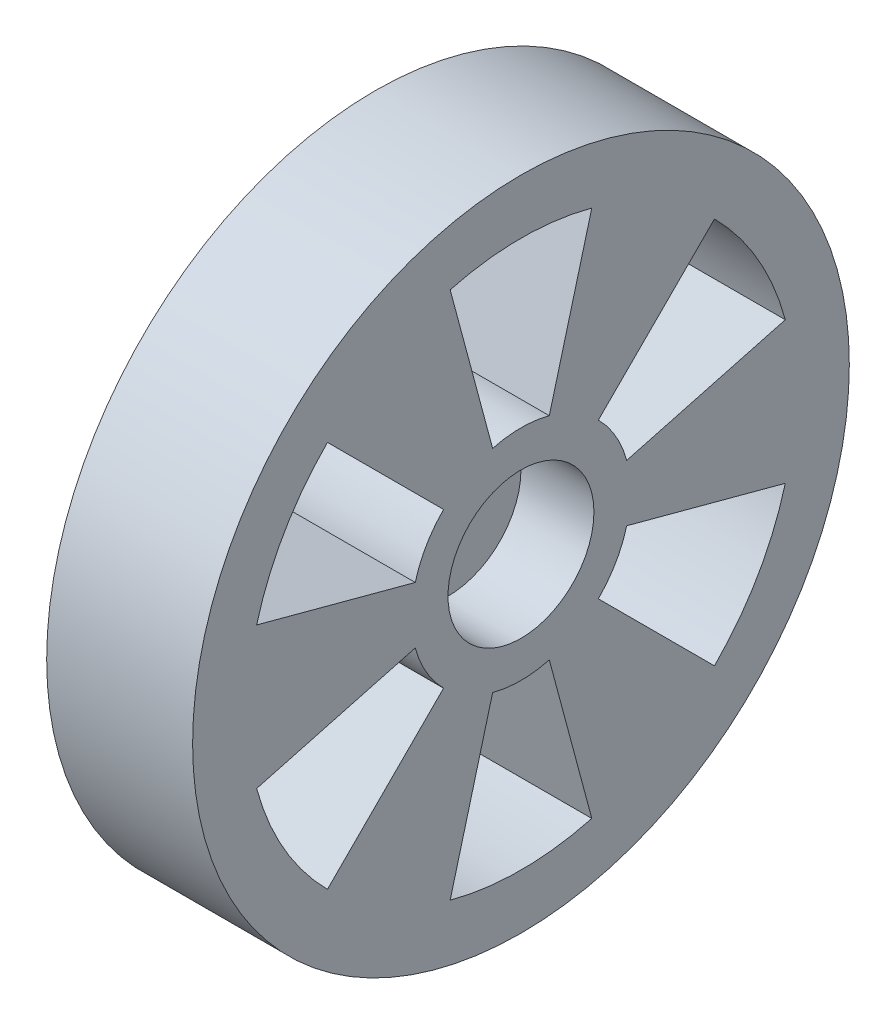
SolidWorks part; units mm, degrees
ref_plane "前视基准面" through (0, 0, 0) normal (0, 0, 1) x (1, 0, 0)
ref_plane "上视基准面" through (0, 0, 0) normal (0, 1, 0) x (1, 0, 0)
ref_plane "右视基准面" through (0, 0, 0) normal (1, 0, 0) x (0, 0, -1)
sketch "草图1" plane through (0, 0, 0) normal (1, 0, 0) x (0, 0, -1)
  circle A0 centre (0, 0) radius 10
extrude "凸台-拉伸1" add sketch "草图1" along normal blind 20
sketch "草图2" plane through (20, 0, 0) normal (1, 0, 0) x (0, 0, -1)
  circle A0 centre (0, 0) radius 45
extrude "凸台-拉伸2" add sketch "草图2" along normal blind 20
sketch "草图3" plane through (20, 0, 0) normal (-1, 0, 0) x (0, 0, 1)
  line L0 (0, 37.5) -> (0, 15) construction
  line L1 (-9.7057, 36.2222) -> (-3.8823, 14.4889)
  line L2 (9.7057, 36.2222) -> (3.8823, 14.4889)
  line L3 (0, -15) -> (0, -37.5) construction
  line L4 (26.5165, 26.5165) -> (10.6066, 10.6066)
  line L5 (36.2222, 9.7057) -> (14.4889, 3.8823)
  line L6 (36.2222, -9.7057) -> (14.4889, -3.8823)
  line L7 (26.5165, -26.5165) -> (10.6066, -10.6066)
  line L8 (9.7057, -36.2222) -> (3.8823, -14.4889)
  line L9 (-9.7057, -36.2222) -> (-3.8823, -14.4889)
  line L10 (-26.5165, -26.5165) -> (-10.6066, -10.6066)
  line L11 (-36.2222, -9.7057) -> (-14.4889, -3.8823)
  line L12 (-36.2222, 9.7057) -> (-14.4889, 3.8823)
  line L13 (-26.5165, 26.5165) -> (-10.6066, 10.6066)
  arc A0 (3.8823, 14.4889) -> (-3.8823, 14.4889) centre (0, 0) ccw
  arc A1 (9.7057, 36.2222) -> (-9.7057, 36.2222) centre (0, 0) ccw
  arc A2 (36.2222, 9.7057) -> (26.5165, 26.5165) centre (0, 0) ccw
  arc A3 (14.4889, 3.8823) -> (10.6066, 10.6066) centre (0, 0) ccw
  arc A4 (26.5165, -26.5165) -> (36.2222, -9.7057) centre (0, 0) ccw
  arc A5 (10.6066, -10.6066) -> (14.4889, -3.8823) centre (0, 0) ccw
  arc A6 (-9.7057, -36.2222) -> (9.7057, -36.2222) centre (0, 0) ccw
  arc A7 (-3.8823, -14.4889) -> (3.8823, -14.4889) centre (0, 0) ccw
  arc A8 (-36.2222, -9.7057) -> (-26.5165, -26.5165) centre (0, 0) ccw
  arc A9 (-14.4889, -3.8823) -> (-10.6066, -10.6066) centre (0, 0) ccw
  arc A10 (-26.5165, 26.5165) -> (-36.2222, 9.7057) centre (0, 0) ccw
  arc A11 (-10.6066, 10.6066) -> (-14.4889, 3.8823) centre (0, 0) ccw
  point P33 (0, 0)
  dimension "D1" = 75
  dimension "D2" = 30
  dimension "D3" = 15
  dimension "D4" = 6
extrude "切除-拉伸1" cut sketch "草图3" against normal blind 20
sketch "草图4" plane through (40, 0, 0) normal (1, 0, 0) x (0, 0, -1)
  circle A0 centre (0, 0) radius 10
extrude "切除-拉伸2" cut sketch "草图4" against normal blind 10
